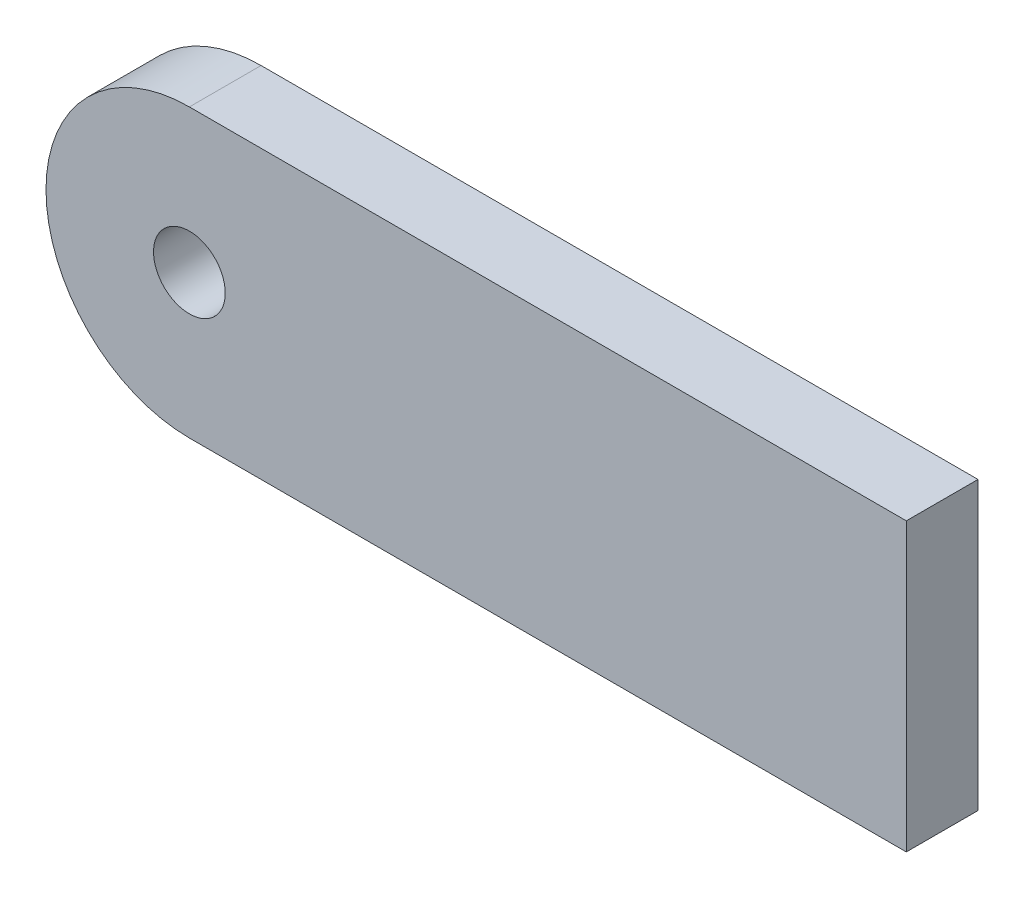
SolidWorks part; units mm, degrees
ref_plane "Front Plane" through (0, 0, 0) normal (0, 0, 1) x (1, 0, 0)
ref_plane "Top Plane" through (0, 0, 0) normal (0, 1, 0) x (1, 0, 0)
ref_plane "Right Plane" through (0, 0, 0) normal (1, 0, 0) x (0, 0, -1)
sketch "Sketch1" plane through (0, 0, 0) normal (0, 0, 1) x (1, 0, 0)
  line L1 (0, 0) -> (-31.75, 0)
  line L2 (0, 0) -> (0, -12.7)
  line L3 (0, -12.7) -> (-31.75, -12.7)
  arc A0 (-31.75, 0) -> (-31.75, -12.7) centre (-31.75, -6.35) ccw
  circle A1 centre (-31.75, -6.35) radius 1.5875
  dimension "D3" = 3.175
  dimension "D1" = 12.7
  dimension "D2" = 31.75
extrude "Boss-Extrude1" add sketch "Sketch1" along normal blind 3.175
